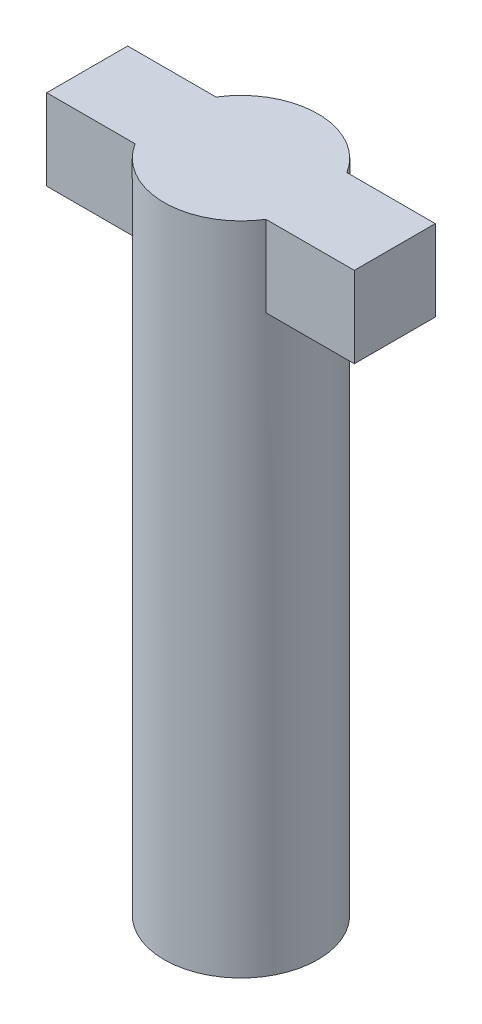
SolidWorks part; units mm, degrees
ref_plane "Front Plane" through (0, 0, 0) normal (0, 0, 1) x (1, 0, 0)
ref_plane "Top Plane" through (0, 0, 0) normal (0, 1, 0) x (1, 0, 0)
ref_plane "Right Plane" through (0, 0, 0) normal (1, 0, 0) x (0, 0, -1)
sketch "Sketch1" plane through (0, 0, 0) normal (0, 1, 0) x (1, 0, 0)
  circle A0 centre (0, 0) radius 0.95
  dimension "D1" = 1.9
extrude "Body" add sketch "Sketch1" along normal blind 8.1
sketch "Sketch2" plane through (0, 8.1, 0) normal (0, 1, 0) x (1, 0, 0)
  line L0 (0, 0) -> (-1.9, 0) construction
  line L1 (0, 0.5) -> (-1.9, 0.5)
  line L2 (0, -0.5) -> (-1.9, -0.5)
  line L3 (-1.9, 0.5) -> (-1.9, -0.5)
  line L4 (0, 0) -> (0, 0.2952) construction
  line L5 (0, 0) -> (1.9, 0) construction
  line L6 (0, -0.5) -> (1.9, -0.5)
  line L7 (1.9, 0.5) -> (1.9, -0.5)
  line L8 (0, 0.5) -> (1.9, 0.5)
  circle A0 centre (0, 0) radius 0.95 construction
  circle A1 centre (0, 0) radius 0.95
  circle M6 centre (0, 0) radius 0.95
  dimension "D1" = 1.9
  dimension "D2" = 0.5
  dimension "D3" = 0.5
extrude "Lock" add sketch "Sketch2" against normal blind 1 contours L1 L3 L2 M6 | L8 L6 L7 M6
equation "\"BoltD\"=2mm"
equation "\"SmallScrewD\"=1.2mm"
equation "\"SmallScrewHatD\"=2mm"
equation "\"TubeOuterD\"=1.2mm"
equation "\"BasicPulleyD\"=15mm"
equation "\"GrooveDepth\"=0.7mm"
equation "\"Cable1D\"=0.4mm"
equation "\"Cable2D\"=0.3mm"
equation "\"BallBearingInnerD\"=2mm"
equation "\"BallBearingOuterD\"=4mm"
equation "\"D1@Sketch1\"=\"BallBearingInnerD\"-0.1"
equation "\"BoltHatD\"=3.2mm"
equation "\"BallBearingThickness\"=2mm"
equation "\"HumerusL\"=37.2mm"
equation "\"HumerusElbowSidePulleyD\"=10mm"
equation "\"RadiusL\"=68.1mm"
equation "\"Finger1L\"=120mm"
equation "\"Finger2L\"=100mm"
equation "\"Finger3L\"=80mm"
equation "\"ElbowExtendedAngle\"=140deg"
equation "\"ElbowFlexedAngle\"=38deg"
equation "\"BearingCapD\"=12mm"
equation "\"TubeClipW\"=1.5mm"
equation "\"TubeClipH\"=1.5mm"
equation "\"TubeClipLock_SideL\"=1.5mm"
equation "\"TubeClipLock_W\"=0.7mm"
equation "\"Digit5ExtendedAngle\"=80deg"
equation "\"Digit5FlexedAngle\"=24deg"
equation "\"Digit4ExtendedAngle\"=108deg"
equation "\"Digit4FlexedAngle\"=34deg"
equation "\"Digit3ExtendedAngle\"=145deg"
equation "\"Digit3FlexedAngle\"=44deg"
equation "\"NutD\"=3.9mm"
equation "\"XL330_M077_T_FrameBoltD\"=1.6mm"
equation "\"XL330_M077_T_FrameBoltHatD\"=2.9mm"
equation "\"XL330_M077_T_FrameNutD\"=2.5mm"
equation "\"KST_ServoShaftBoltD\"=2.5mm"
equation "\"KST_ServoShaftBoltHatD\"=5.2mm"
equation "\"XL330_M077_T_HornScrewD\"=1.9mm"
equation "\"XL330_M077_T_HornScrewHatD\"=3.3mm"
